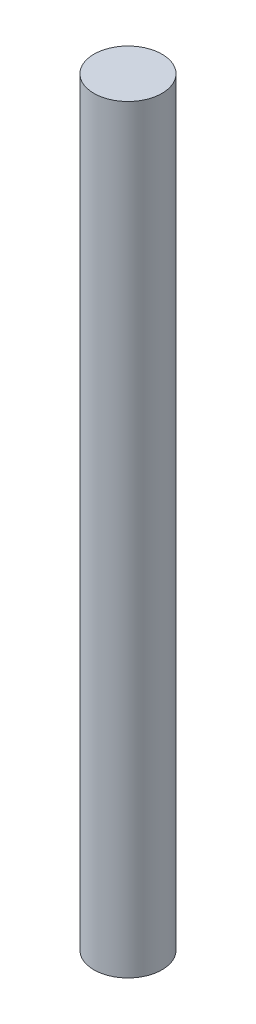
SolidWorks part; units mm, degrees
ref_plane "Front Plane" through (0, 0, 0) normal (0, 0, 1) x (1, 0, 0)
ref_plane "Top Plane" through (0, 0, 0) normal (0, 1, 0) x (1, 0, 0)
ref_plane "Right Plane" through (0, 0, 0) normal (1, 0, 0) x (0, 0, -1)
sketch "Sketch2" plane through (0, 0, 0) normal (0, 1, 0) x (1, 0, 0)
  circle A0 centre (0, 0) radius 1.075
  dimension "D1" = 2.15
extrude "Boss-Extrude1" add sketch "Sketch2" along normal blind 24
